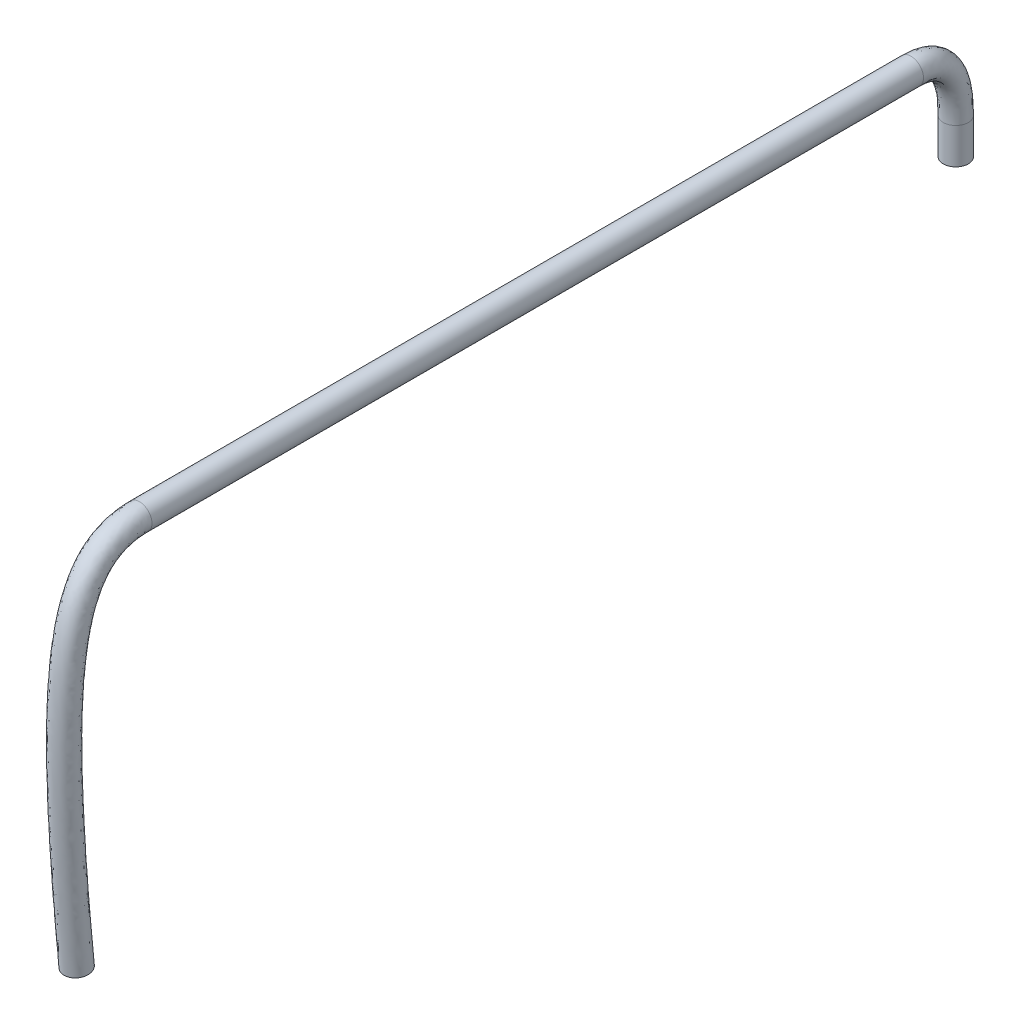
SolidWorks part; units mm, degrees
ref_plane "Front" through (0, 0, 0) normal (0, 0, 1) x (1, 0, 0)
ref_plane "Top" through (0, 0, 0) normal (0, 1, 0) x (1, 0, 0)
ref_plane "Right" through (0, 0, 0) normal (1, 0, 0) x (0, 0, -1)
sketch "Sketch1" plane through (0, 0, 0) normal (1, 0, 0) x (0, 0, -1)
  line L2 (0, 0) -> (0, 2)
  line L4 (-2.5, 5.4) -> (-45.5, 5.4)
  spline S0 degree 3 poles (0, 2) (0, 3.6742) (-0.4303, 5.4) (-2.5, 5.4) knots 0 0 0 0 1 1 1 1
  spline S1 degree 3 poles (-45.5, 5.4) (-49.9577, 5.4) (-50.3735, -0.2526) (-49, -14.6) knots 0 0 0 0 1 1 1 1
  dimension "D4" = 20
  dimension "D6" = 2.5
  dimension "D1" = 2
  dimension "D2" = 5.4
  dimension "D3" = 43
  dimension "D5" = 3.5
sketch "Sketch2" plane through (0, 0, 0) normal (0, 1, 0) x (1, 0, 0)
  circle A0 centre (0, 0) radius 0.7
  dimension "D1" = 1.4
sweep "Sweep1" add profiles "Sketch2" path "Sketch1"
